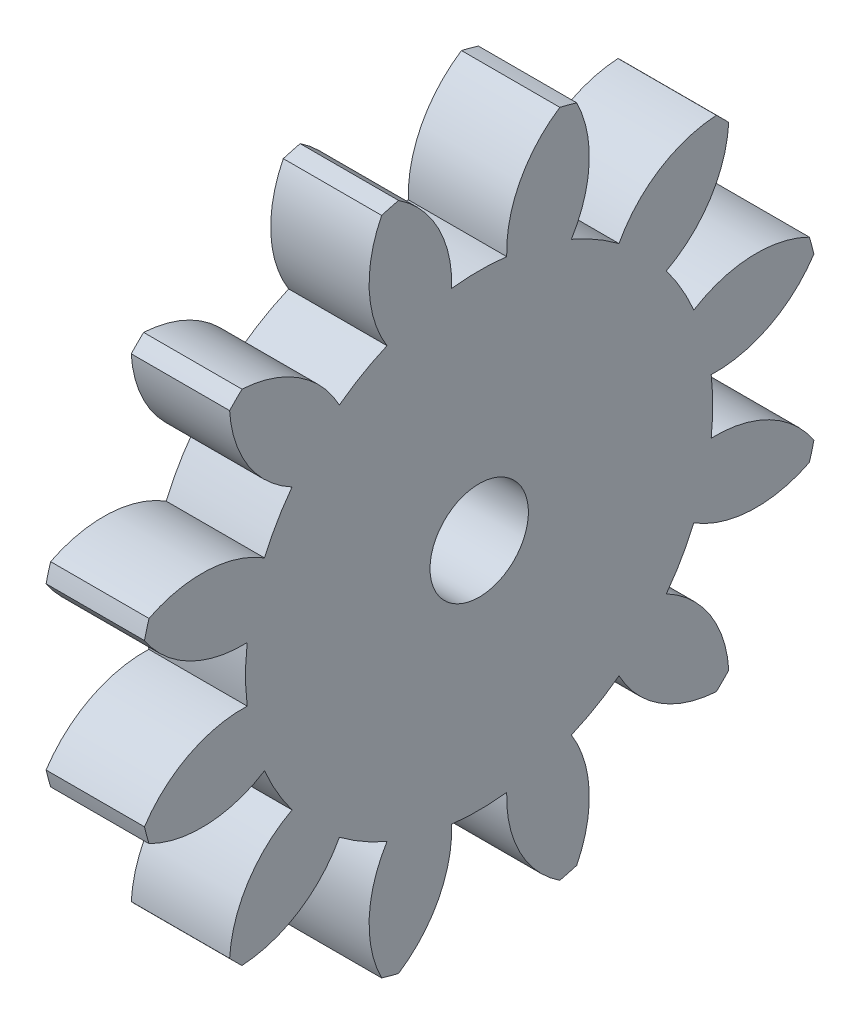
SolidWorks part; units mm, degrees
ref_plane "Plane1" through (0, 0, 0) normal (0, 0, 1) x (1, 0, 0)
ref_plane "Plane2" through (0, 0, 0) normal (0, 1, 0) x (1, 0, 0)
ref_plane "Plane3" through (0, 0, 0) normal (1, 0, 0) x (0, 0, -1)
sketch "HoldingSke" plane through (0, 0, 0) normal (0, 1, 0) x (1, 0, 0)
  line L0 (0, 0) -> (99.3798, -21.1238)
  line L1 (-15, 0) -> (100, 0) construction
  line L2 (0, 0) -> (-2.1039, 2.3779)
  line L3 (0, 0) -> (-11.863, 4.5341)
  line L4 (0, 0) -> (8.4473, 1.7955)
  line L5 (0, 0) -> (-47.5972, -17.7524)
  line L6 (0, 0) -> (-10.5278, -7.1032)
  line L7 (-2.1039, 2.3779) -> (8.8308, 51.9871)
  line L8 (-76.2, 54.61) -> (-61.976, 54.61)
  line L9 (-71.009, 38.7566) -> (-53.1078, 45.2721)
  line L10 (-76.2, 71.12) -> (104.1128, 71.12)
  line L11 (0, 0) -> (-12.7, 0)
  line L12 (-76.2, 101.6) -> (-75.9714, 101.6)
  line L13 (24.9733, 27.94) -> (52.9518, 28.4284)
  line L14 (24.9733, 27.94) -> (24.9746, 27.94)
  line L15 (24.9733, 27.94) -> (100.4006, 29.5858)
  circle A0 centre (0, 0) radius 6.35
  circle A1 centre (0, 0) radius 30.1612
  circle A2 centre (0, 0) radius 38.1
  circle A3 centre (0, 0) radius 6.35
sketch "BasProSke" plane through (0, 0, 0) normal (0, 1, 0) x (1, 0, 0)
  line L0 (-10, 0) -> (60, 0) construction
  line L1 (0, 0) -> (0, 44.45)
  line L2 (0, 0) -> (12.7, 0)
  line L3 (12.7, 0) -> (12.7, 44.45)
  line L4 (12.7, 44.45) -> (0, 44.45)
revolve "Base-Revolve" add sketch "BasProSke" angle 360 about L0
sketch "TooCutSke" plane through (0, 0, 0) normal (1, 0, 0) x (0, 0, -1)
  line L1 (0, 0) -> (0, 107) construction
  line L2 (0, 0) -> (-5.3725, 37.7193) construction
  line L3 (0, 0) -> (-19.5794, 73.0714) construction
  line L4 (-5.3725, 37.7193) -> (-9.7897, 36.5357) construction
  arc A0 (3.5522, 29.9513) -> (-3.5522, 29.9513) centre (0, 0) ccw
  arc A1 (10.4397, 43.2328) -> (-10.4397, 43.2328) centre (0, 0) ccw
  circle A2 centre (0, 0) radius 38.1 construction
  circle A3 centre (0, 0) radius 35.8023 construction
  arc A4 (-3.5522, 29.9513) -> (-10.4397, 43.2328) centre (-18.7831, 30.4795) ccw
  arc A5 (10.4397, 43.2328) -> (3.5522, 29.9513) centre (18.7831, 30.4795) ccw
extrude "ToothCut" cut sketch "TooCutSke" along normal through all
fillet "Breaks" [suppressed] radius 0.127
fillet "RootFillets" [suppressed] radius 1.5888
pattern_circular "TeethCuts" count 12 every 30 about axis through (-10, 0, 0) along (1, 0, 0) of "ToothCut", "RootFillets", "Breaks"
sketch "HubNeaOneSke" plane through (0, 0, 0) normal (-1, 0, 0) x (0, 0, 1)
  circle A0 centre (0, 0) radius 30.1612
extrude "HubNearOne" [suppressed] add sketch "HubNeaOneSke" along normal blind 38.1001
sketch "HubNeaBotSke" plane through (0, 0, 0) normal (-1, 0, 0) x (0, 0, 1)
  circle A0 centre (0, 0) radius 30.1612
extrude "HubNearBoth" [suppressed] add sketch "HubNeaBotSke" along normal blind 19.05
ref_plane "FarPln" through (12.7, 0, 0) normal (1, 0, 0) x (0, 0, -1)
sketch "HubFarSke" plane through (12.7, 0, 0) normal (1, 0, 0) x (0, 0, -1)
  circle A0 centre (0, 0) radius 30.1612
extrude "HubFar" [suppressed] add sketch "HubFarSke" along normal blind 19.05
sketch "BorSke" plane through (0, 0, 0) normal (1, 0, 0) x (0, 0, -1)
  circle A0 centre (0, 0) radius 6.35
extrude "Bore" cut sketch "BorSke" along normal mid plane 101.6001
sketch "KeySke" plane through (0, 0, 0) normal (1, 0, 0) x (0, 0, -1)
  line L0 (-1.5875, 0) -> (-1.5875, 7.874)
  line L1 (-1.5875, 7.874) -> (1.5875, 7.874)
  line L2 (1.5875, 7.874) -> (1.5875, 0)
  line L3 (0, 0) -> (0, 34) construction
  line L4 (-1.5875, 0) -> (1.5875, 0)
extrude "Keyway" [suppressed] cut sketch "KeySke" along normal mid plane 101.6001
pattern_circular "Keyway2" [suppressed] count 2 every 90 about axis through (-10, 0, 0) along (1, 0, 0)
equation "' \"Pitch@HoldingSke\" = 4"
equation "' \"Num_teeth@HoldingSke\" = 12"
equation "' \"Ap@HoldingSke\" =  20"
equation "' \"Ap@HoldingSke\" = 20"
equation "' \"Width@HoldingSke\" = 0.5"
equation "' \"Hub_dia@HoldingSke\"= 1"
equation "' \"Hub_dia@HoldingSke\" = 1"
equation "' \"Overall_len@HoldingSke\" = 1.0"
equation "' \"Bore@HoldingSke\" = 0.75"
equation "' \"T_dim@HoldingSke\" = 0.85"
equation "' \"Width@KeySke\" = 0.25"
equation "' \"Show_teeth@HoldingSke\" = 13"
equation "' \"Backlash@HoldingSke\" = 0.009"
equation "' \"Addendum_fac@HoldingSke\" = 1.0"
equation "' \"Dedendum_fac@HoldingSke\" = 1.25"
equation "' \"Dedendum_add@HoldingSke\" = 0.00005"
equation "' \"Clearance_fac@HoldingSke\" = 0.25"
equation "' \"Pitch@HoldingSke\" = 0.5"
equation "' \"Num_teeth@HoldingSke\" = 23"
equation "' \"Show_teeth@HoldingSke\" = 23"
equation "' \"Backlash@HoldingSke\" = 0.0375"
equation "\"Overcut_dia@TooCutSke\" = (\"Num_teeth@HoldingSke\" + 2 * \"Addendum_fac@HoldingSke\") / \"Pitch@HoldingSke\" + 0.002"
equation "\"Pitch_dia@TooCutSke\" = \"Num_teeth@HoldingSke\" / \"Pitch@HoldingSke\""
equation "\"Base_dia@TooCutSke\" = \"Num_teeth@HoldingSke\" / \"Pitch@HoldingSke\" * cos((\"Ap@HoldingSke\"  * 3.14159265 / 180))"
equation "\"Root_dia@TooCutSke\" = (\"Num_teeth@HoldingSke\" + 2) / \"Pitch@HoldingSke\" - 2 * (\"Addendum_fac@HoldingSke\" + \"Dedendum_fac@HoldingSke\") / \"Pitch@HoldingSke\" - \"Dedendum_add@HoldingSke\" * 2"
equation "\"Half_ang@TooCutSke\" = 180 / \"Num_teeth@HoldingSke\""
equation "\"Half_CT@TooCutSke\" = \"Num_teeth@HoldingSke\" / \"Pitch@HoldingSke\" * sin((3.14159265 / 2 / \"Num_teeth@HoldingSke\")) / 2 - 7 * \"Backlash@HoldingSke\" / 4"
equation "\"Flank_rad@TooCutSke\" = \"Num_teeth@HoldingSke\" / \"Pitch@HoldingSke\" / 5"
equation "\"Radius@RootFillets\" = \"Clearance_fac@HoldingSke\" / \"Pitch@HoldingSke\" + \"Dedendum_add@HoldingSke\""
equation "\"Break_rad@Breaks\" = 0.02 / \"Pitch@HoldingSke\""
equation "\"Thickness@HoldingSke\" = \"Width@HoldingSke\""
equation "\"OAL@HoldingSke\" = \"Thickness@HoldingSke\""
equation "\"MHD@HoldingSke\" = (\"Num_teeth@HoldingSke\" + 2) / \"Pitch@HoldingSke\" - 2 * (\"Addendum_fac@HoldingSke\" + \"Dedendum_fac@HoldingSke\")  / \"Pitch@HoldingSke\" - \"Dedendum_add@HoldingSke\" * 2"
equation "\"MBD@HoldingSke\" = (\"Num_teeth@HoldingSke\" + 2) / \"Pitch@HoldingSke\" - 2 * (\"Addendum_fac@HoldingSke\" + \"Dedendum_fac@HoldingSke\")  / \"Pitch@HoldingSke\" - \"Dedendum_add@HoldingSke\" * 2 - 0.002"
equation "\"MHD@HoldingSke\" = ((sgn( \"MHD@HoldingSke\" - \"Hub_dia@HoldingSke\" )-1)*( \"MHD@HoldingSke\" - \"Hub_dia@HoldingSke\" ))/-2+ \"Hub_dia@HoldingSke\""
equation "\"MBD@HoldingSke\" = ((sgn( \"MBD@HoldingSke\" - \"Bore@HoldingSke\" )-1)*( \"MBD@HoldingSke\" - \"Bore@HoldingSke\" ))/-2+ \"Bore@HoldingSke\""
equation "\"OAL@HoldingSke\" = ((sgn( \"OAL@HoldingSke\" - \"Overall_len@HoldingSke\" )+1)*( \"OAL@HoldingSke\" - \"Overall_len@HoldingSke\" ))/2 + \"Overall_len@HoldingSke\" + 0.000002"
equation "\"Num_teeth@TeethCuts\" = int( \"Show_teeth@HoldingSke\" ) + 1"
equation "\"Num_teeth@TeethCuts\" = ((sgn( \"Num_teeth@TeethCuts\" - \"Num_teeth@HoldingSke\" )-1)*( \"Num_teeth@TeethCuts\" - \"Num_teeth@HoldingSke\" ))/-2+ \"Num_teeth@HoldingSke\""
equation "\"Num_teeth@TeethCuts\" = ((sgn( \"Num_teeth@TeethCuts\" - 2.0)+1)*( \"Num_teeth@TeethCuts\" - 2.0))/2 +2.0"
equation "\"Angle@TeethCuts\" = 360.0 / \"Num_teeth@HoldingSke\""
equation "\"Diameter@BasProSke\" = (\"Num_teeth@HoldingSke\" + 2 * \"Addendum_fac@HoldingSke\") / \"Pitch@HoldingSke\""
equation "\"Thickness@BasProSke\"  = \"Thickness@HoldingSke\""
equation "' \"Fillet_rad@BasProSke\" =  \"Thickness@HoldingSke\" * 0.05"
equation "' \"Fillet_rad@BasProSke\" = \"Thickness@HoldingSke\" * 0.05"
equation "\"MHD@HoldingSke\" = ((sgn( \"MHD@HoldingSke\" - \"Root_dia@TooCutSke\" )-1)*( \"MHD@HoldingSke\" - \"Root_dia@TooCutSke\" ))/-2+ \"Root_dia@TooCutSke\""
equation "\"Diameter@HubNeaOneSke\" = \"MHD@HoldingSke\""
equation "\"Length@HubNearOne\" = \"OAL@HoldingSke\" - \"Thickness@BasProSke\""
equation "\"Diameter@HubNeaBotSke\" = \"MHD@HoldingSke\""
equation "\"Length@HubNearBoth\" = ( \"OAL@HoldingSke\" - \"Thickness@BasProSke\" ) / 2.0"
equation "\"Thickness@FarPln\" = \"Thickness@BasProSke\""
equation "\"Diameter@HubFarSke\" = \"MHD@HoldingSke\""
equation "\"Length@HubFar\" = ( \"OAL@HoldingSke\" - \"Thickness@BasProSke\" ) / 2.0"
equation "\"Diameter@BorSke\" = \"MBD@HoldingSke\""
equation "\"D1@Bore\" = \"OAL@HoldingSke\" * 2.0"
equation "\"D1@Keyway\" = \"OAL@HoldingSke\" * 2.0"
equation "\"Offset@KeySke\" = \"T_dim@HoldingSke\" - \"MBD@HoldingSke\" / 2.0"
